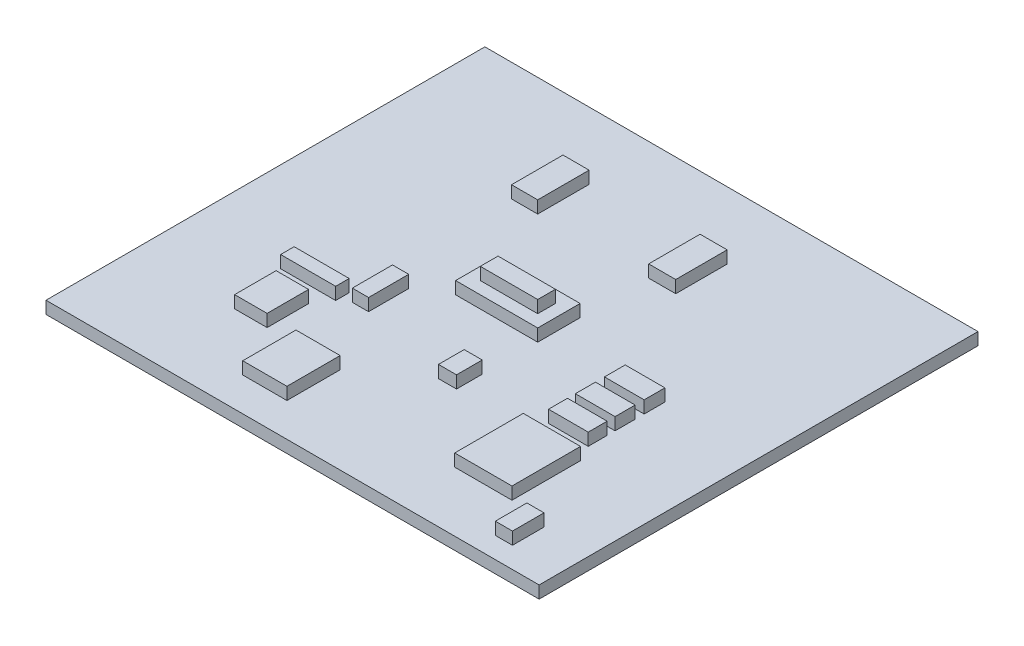
SolidWorks part; units mm, degrees
ref_plane "Alzado" through (0, 0, 0) normal (0, 0, 1) x (1, 0, 0)
ref_plane "Planta" through (0, 0, 0) normal (0, 1, 0) x (1, 0, 0)
ref_plane "Vista lateral" through (0, 0, 0) normal (1, 0, 0) x (0, 0, -1)
sketch "Croquis1" plane through (0, 0, 0) normal (0, 1, 0) x (1, 0, 0)
  line L1 (-32.9489, 13.2347) -> (7.0511, 13.2347)
  line L2 (-32.9489, 13.2347) -> (-32.9489, -22.3653)
  line L3 (-32.9489, -22.3653) -> (7.0511, -22.3653)
  line L4 (7.0511, 13.2347) -> (7.0511, -22.3653)
  dimension "D1" = 35.6
  dimension "D2" = 40
extrude "Saliente-Extruir1" add sketch "Croquis1" along normal blind 1
sketch "Croquis2" plane through (0, 1, 0) normal (0, 1, 0) x (1, 0, 0)
  line L1 (-16.7172, -1.9311) -> (-10.0586, -1.9311)
  line L2 (-16.7172, -1.9311) -> (-16.7172, -5.3702)
  line L3 (-16.7172, -5.3702) -> (-10.0586, -5.3702)
  line L4 (-10.0586, -1.9311) -> (-10.0586, -5.3702)
  line L5 (-4.6439, -11.9556) -> (0, -11.9556)
  line L6 (-4.6439, -11.9556) -> (-4.6439, -17.5166)
  line L7 (-4.6439, -17.5166) -> (0, -17.5166)
  line L8 (0, -11.9556) -> (0, -17.5166)
  line L9 (-24.6929, -11.9556) -> (-22.0587, -11.9556)
  line L10 (-24.6929, -11.9556) -> (-24.6929, -15.3215)
  line L11 (-24.6929, -15.3215) -> (-22.0587, -15.3215)
  line L12 (-22.0587, -11.9556) -> (-22.0587, -15.3215)
  line L13 (-25.6441, -9.5409) -> (-21.1807, -9.5409)
  line L14 (-25.6441, -9.5409) -> (-25.6441, -10.6385)
  line L15 (-25.6441, -10.6385) -> (-21.1807, -10.6385)
  line L16 (-21.1807, -9.5409) -> (-21.1807, -10.6385)
  line L17 (-20.3758, -6.8336) -> (-19.0587, -6.8336)
  line L18 (-20.3758, -6.8336) -> (-20.3758, -10.0897)
  line L19 (-20.3758, -10.0897) -> (-19.0587, -10.0897)
  line L20 (-19.0587, -6.8336) -> (-19.0587, -10.0897)
  line L21 (-19.7172, -15.3215) -> (-16.1318, -15.3215)
  line L22 (-19.7172, -15.3215) -> (-19.7172, -19.6386)
  line L23 (-19.7172, -19.6386) -> (-16.1318, -19.6386)
  line L24 (-16.1318, -15.3215) -> (-16.1318, -19.6386)
  line L25 (-21.1807, 7.8007) -> (-19.0587, 7.8007)
  line L26 (-21.1807, 7.8007) -> (-21.1807, 3.6299)
  line L27 (-21.1807, 3.6299) -> (-19.0587, 3.6299)
  line L28 (-19.0587, 7.8007) -> (-19.0587, 3.6299)
  line L29 (-10.0586, 7.8007) -> (-7.8635, 7.8007)
  line L30 (-10.0586, 7.8007) -> (-10.0586, 3.6299)
  line L31 (-10.0586, 3.6299) -> (-7.8635, 3.6299)
  line L32 (-7.8635, 7.8007) -> (-7.8635, 3.6299)
  line L33 (1.7952, -18.102) -> (3.1854, -18.102)
  line L34 (1.7952, -18.102) -> (1.7952, -20.663)
  line L35 (1.7952, -20.663) -> (3.1854, -20.663)
  line L36 (3.1854, -18.102) -> (3.1854, -20.663)
  line L37 (-3.9122, -9.1019) -> (-0.6927, -9.1019)
  line L38 (-3.9122, -9.1019) -> (-3.9122, -10.6385)
  line L39 (-3.9122, -10.6385) -> (-0.6927, -10.6385)
  line L40 (-0.6927, -9.1019) -> (-0.6927, -10.6385)
  line L41 (-3.9122, -6.8336) -> (-0.6927, -6.8336)
  line L42 (-3.9122, -6.8336) -> (-3.9122, -8.4617)
  line L43 (-3.9122, -8.4617) -> (-0.6927, -8.4617)
  line L44 (-0.6927, -6.8336) -> (-0.6927, -8.4617)
  line L45 (-3.9122, -4.4189) -> (-0.6927, -4.4189)
  line L46 (-3.9122, -4.4189) -> (-3.9122, -6.1019)
  line L47 (-3.9122, -6.1019) -> (-0.6927, -6.1019)
  line L48 (-0.6927, -4.4189) -> (-0.6927, -6.1019)
  line L49 (-11.522, -9.8702) -> (-10.0586, -9.8702)
  line L50 (-11.522, -9.8702) -> (-11.522, -11.9556)
  line L51 (-11.522, -11.9556) -> (-10.0586, -11.9556)
  line L52 (-10.0586, -9.8702) -> (-10.0586, -11.9556)
extrude "Saliente-Extruir2" add sketch "Croquis2" along normal blind 1
sketch "Croquis3" plane through (0, 2, 0) normal (0, 1, 0) x (1, 0, 0)
  line L14 (-11.0586, -4.3702) -> (-11.0586, -2.9311)
  line L15 (-15.7172, -4.3702) -> (-11.0586, -4.3702)
  line L16 (-15.7172, -2.9311) -> (-15.7172, -4.3702)
  line L17 (-11.0586, -2.9311) -> (-15.7172, -2.9311)
  line L18 (-11.0586, -4.3702) -> (-11.0586, -2.9311)
  line L19 (-15.7172, -4.3702) -> (-11.0586, -4.3702)
  line L20 (-15.7172, -2.9311) -> (-15.7172, -4.3702)
  line L21 (-11.0586, -2.9311) -> (-15.7172, -2.9311)
  dimension "D1" = 1
extrude "Saliente-Extruir3" add sketch "Croquis3" along normal blind 1
